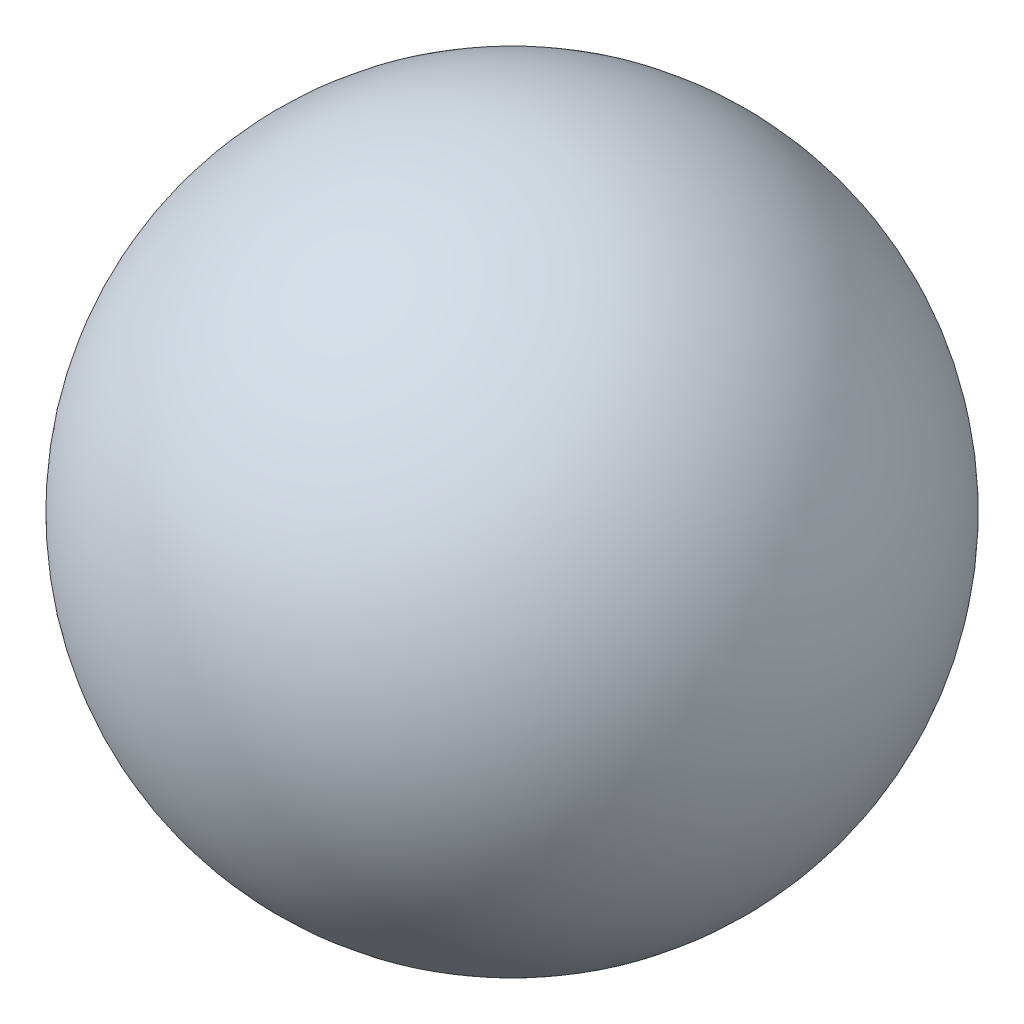
SolidWorks part; units mm, degrees
ref_plane "Front Plane" through (0, 0, 0) normal (0, 0, 1) x (1, 0, 0)
ref_plane "Top Plane" through (0, 0, 0) normal (0, 1, 0) x (1, 0, 0)
ref_plane "Right Plane" through (0, 0, 0) normal (1, 0, 0) x (0, 0, -1)
sketch "Sketch1" plane through (0, 0, 0) normal (0, 0, 1) x (1, 0, 0)
  line L0 (0, 20) -> (0, -20)
  arc A0 (0, -20) -> (0, 20) centre (0, 0) ccw
revolve "Revolve1" add sketch "Sketch1" angle 360 about L0
